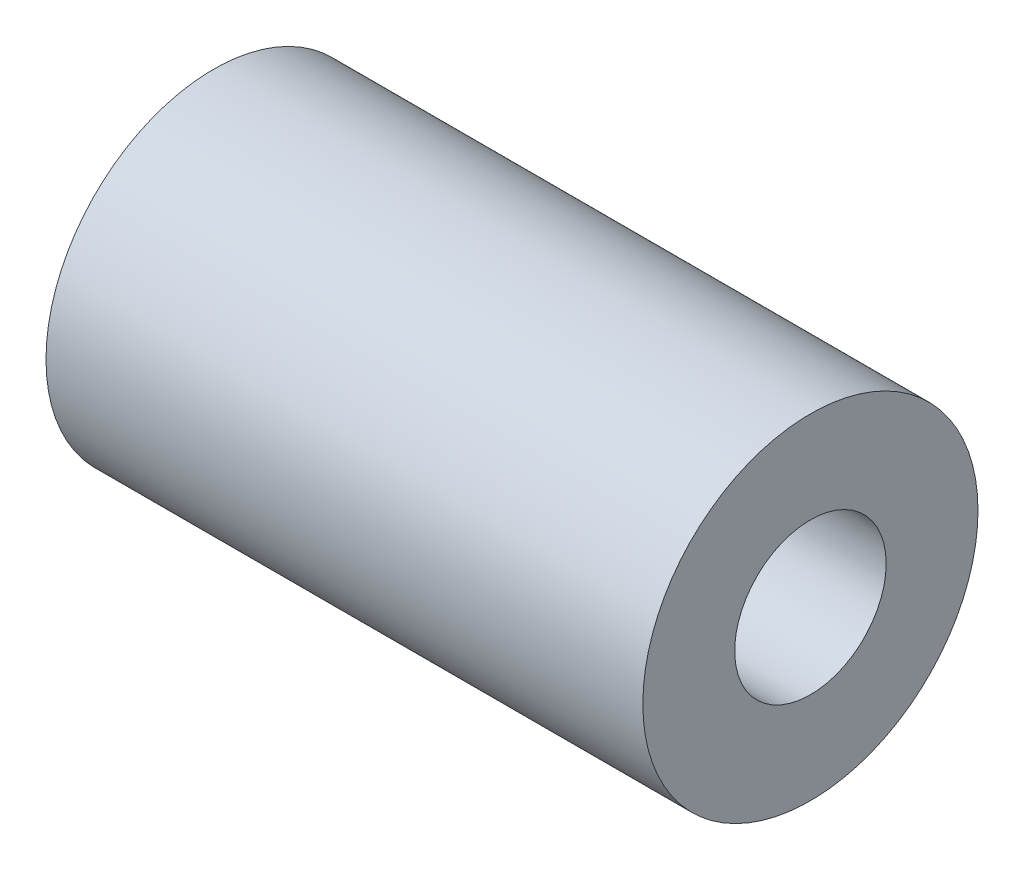
SolidWorks part; units mm, degrees
ref_plane "前视基准面" through (0, 0, 0) normal (0, 0, 1) x (1, 0, 0)
ref_plane "上视基准面" through (0, 0, 0) normal (0, 1, 0) x (1, 0, 0)
ref_plane "右视基准面" through (0, 0, 0) normal (1, 0, 0) x (0, 0, -1)
sketch "草图1" plane through (0, 0, 0) normal (1, 0, 0) x (0, 0, -1)
  circle A0 centre (0, 0) radius 1.65
  circle A1 centre (0, 0) radius 3.65
  dimension "D1" = 3.3
  dimension "D2" = 2
extrude "凸台-拉伸1" add sketch "草图1" along normal blind 13
